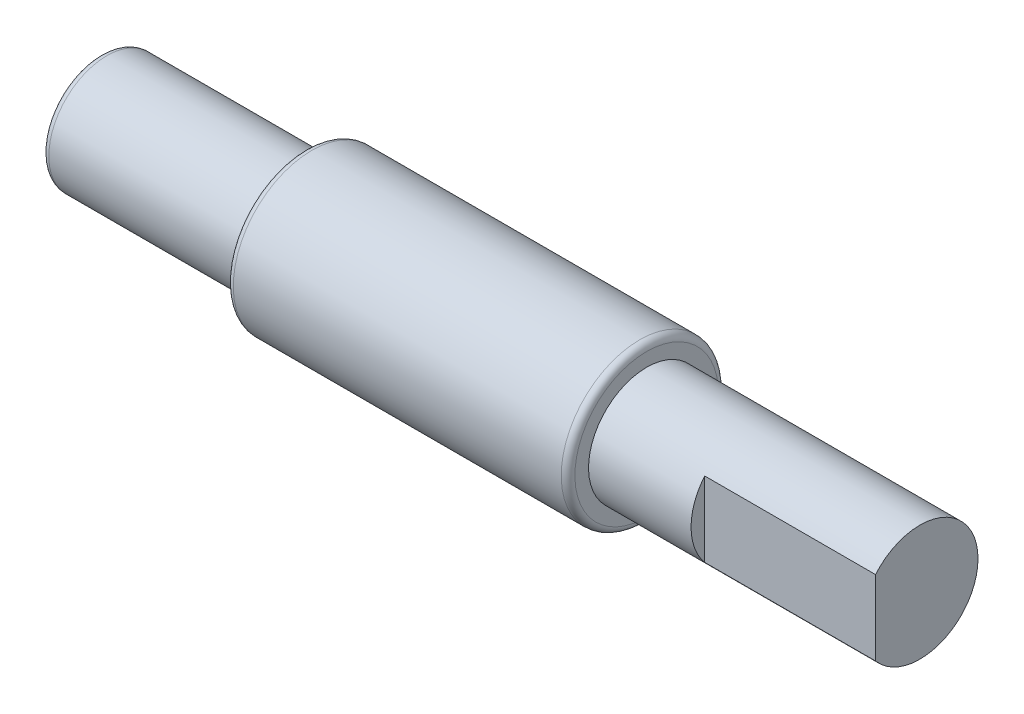
SolidWorks part; units mm, degrees
ref_plane "Plan de face" through (0, 0, 0) normal (0, 0, 1) x (1, 0, 0)
ref_plane "Plan de dessus" through (0, 0, 0) normal (0, 1, 0) x (1, 0, 0)
ref_plane "Plan de droite" through (0, 0, 0) normal (1, 0, 0) x (0, 0, -1)
sketch "Esquisse1" plane through (0, 0, 0) normal (0, 0, 1) x (1, 0, 0)
  line L0 (0, 0) -> (-120, 0)
  line L1 (-120, 0) -> (-120, 7.5)
  line L2 (-119, 8.5) -> (-90, 8.5)
  line L3 (-90, 8.5) -> (-90, 10.5)
  line L4 (-89, 11.5) -> (-41, 11.5)
  line L5 (-40, 10.5) -> (-40, 8.5)
  line L6 (-40, 8.5) -> (0, 8.5)
  line L7 (0, 8.5) -> (0, 0)
  arc A0 (-90, 10.5) -> (-89, 11.5) centre (-89, 10.5) cw
  arc A1 (-40, 10.5) -> (-41, 11.5) centre (-41, 10.5) ccw
  arc A2 (-119, 8.5) -> (-120, 7.5) centre (-119, 7.5) ccw
  point P11 (-90, 11.5)
  point P14 (-40, 11.5)
  point P17 (-120, 8.5)
  dimension "D7" = 1
  dimension "D8" = 1
  dimension "D9" = 1
  dimension "D1" = 120
  dimension "D2" = 50
  dimension "D3" = 30
  dimension "D4" = 8.5
  dimension "D5" = 3
  dimension "D6" = 3
revolve "Révolution1" add sketch "Esquisse1" angle 360 about L0
sketch "Esquisse6" plane through (0, 0, 0) normal (1, 0, 0) x (0, 0, -1)
  line L1 (-6.5, 9.405) -> (-6.5, -10.595)
  line L2 (-6.5, -10.595) -> (-12.3253, -10.595)
  line L3 (-12.3253, -10.595) -> (-12.3253, 19.405)
  line L4 (-12.3253, 19.405) -> (-6.5, 19.405)
  line L5 (-6.5, 19.405) -> (-6.5, 9.405)
  dimension "D1" = 6.5
  dimension "D2" = 20
  dimension "D3" = 10
extrude "Enlèv. mat.-Extru.6" cut sketch "Esquisse6" against normal blind 25
